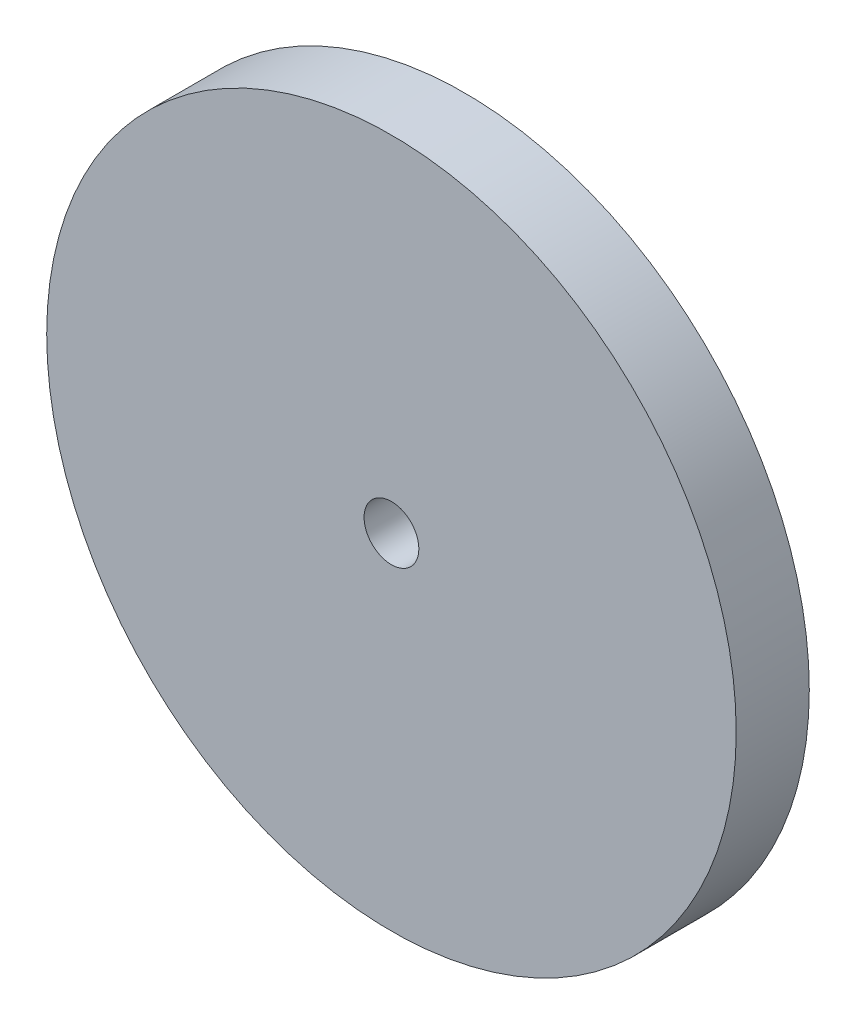
SolidWorks part; units mm, degrees
ref_plane "Front Plane" through (0, 0, 0) normal (0, 0, 1) x (1, 0, 0)
ref_plane "Top Plane" through (0, 0, 0) normal (0, 1, 0) x (1, 0, 0)
ref_plane "Right Plane" through (0, 0, 0) normal (1, 0, 0) x (0, 0, -1)
sketch "Sketch1" plane through (0, 0, 0) normal (0, 0, 1) x (1, 0, 0)
  circle A0 centre (0, 0) radius 28.3
  dimension "D1" = 56.6
extrude "Boss-Extrude1" add sketch "Sketch1" along normal blind 6
hole_wizard "#16 (0.177) Diameter Hole1" positions "Sketch10" profile "Sketch11" hole size "#16" standard "Ansi Inch" end condition through all
sketch "Sketch10" plane through (0, 0, 6) normal (0, 0, 1) x (1, 0, 0)
  point P1 (0, 0)
sketch "Sketch11" plane through (0, 0, 6) normal (1, 0, 0) x (0, -1, 0)
  line L0 (0, 0) -> (0, 6)
  line L1 (0, 6) -> (2.2479, 6)
  line L2 (2.2479, 6) -> (2.2479, 0)
  line L5 (2.2479, 0) -> (0, 0)
  line L11 (0, -6.35) -> (0, 107.95) construction
  dimension "Thru Hole Dia." = 4.4958
  dimension "Thru Hole Depth" = 6
